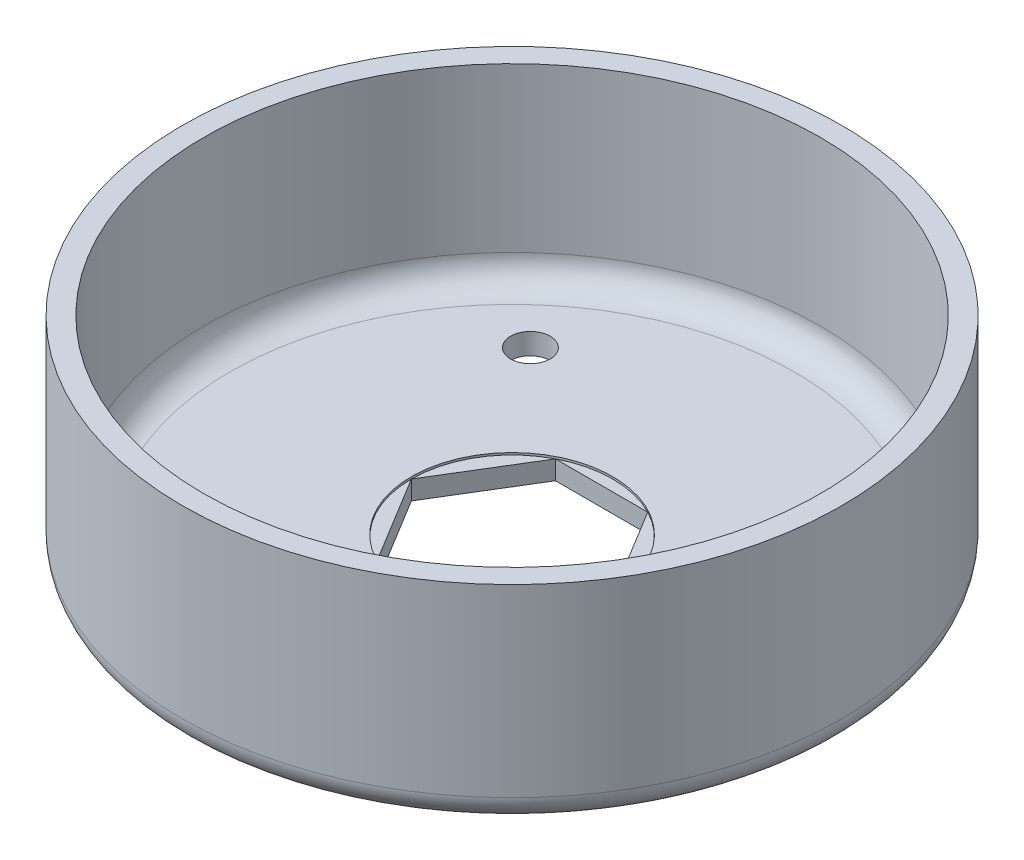
SolidWorks part; units mm, degrees
material "Alloy Steel"
ref_plane "Front Plane" through (0, 0, 0) normal (0, 0, 1) x (1, 0, 0)
ref_plane "Top Plane" through (0, 0, 0) normal (0, 1, 0) x (1, 0, 0)
ref_plane "Right Plane" through (0, 0, 0) normal (1, 0, 0) x (0, 0, -1)
other "Configuration Table"
sketch "Sketch1" plane through (0, 0, 0) normal (0, 1, 0) x (1, 0, 0)
  circle A0 centre (0, 0) radius 39.6875
  dimension "D1" = 79.375
extrude "Boss-Extrude1" add sketch "Sketch1" along normal blind 25.4
shell "Shell1" thickness 2.54
sketch "Sketch2" plane through (0, 25.4, 0) normal (0, 1, 0) x (1, 0, 0)
  line L0 (-5.5562, 10.7765) -> (5.5562, 10.7765)
  line L1 (5.5562, 10.7765) -> (12.1246, 0)
  line L2 (12.1246, 0) -> (5.5562, -10.7765)
  line L3 (5.5562, -10.7765) -> (-5.5562, -10.7765)
  line L4 (-5.5562, -10.7765) -> (-12.1246, 0)
  line L5 (-12.1246, 0) -> (-5.5562, 10.7765)
  circle A0 centre (0, 0) radius 12.1246 construction
  dimension "D1" = 11.1125
  dimension "D2" = 11.1125
extrude "Cut-Extrude1" cut sketch "Sketch2" against normal through all
sketch "Sketch4" plane through (0, 2.54, 0) normal (0, 1, 0) x (1, 0, 0)
  circle A0 centre (0, 0) radius 12.1246
extrude "Cut-Extrude2" cut sketch "Sketch4" against normal blind 0.254
fillet "Fillet1" radius 3.175 1 edges at (0, 0, 39.6875)
sketch "Sketch5" plane through (0, 0, 0) normal (0, -1, 0) x (1, 0, 0)
  line L1 (5.5562, -10.7765) -> (-5.5562, -10.7765) construction
  circle A0 centre (19.8668, 20.619) radius 2.3813
  circle A1 centre (-18.4131, 20.619) radius 2.3813
  circle A2 centre (-18.4131, -20.619) radius 2.3813
  circle A3 centre (19.8668, -17.1265) radius 2.3813
  dimension "D1" = 4.7625
  dimension "D2" = 9.8425
  dimension "D3" = 9.8425
  dimension "D4" = 6.35
extrude "Cut-Extrude3" cut sketch "Sketch5" against normal through all
fillet "Fillet2" radius 3.175 1 edges at (0, 2.54, 37.1475)
